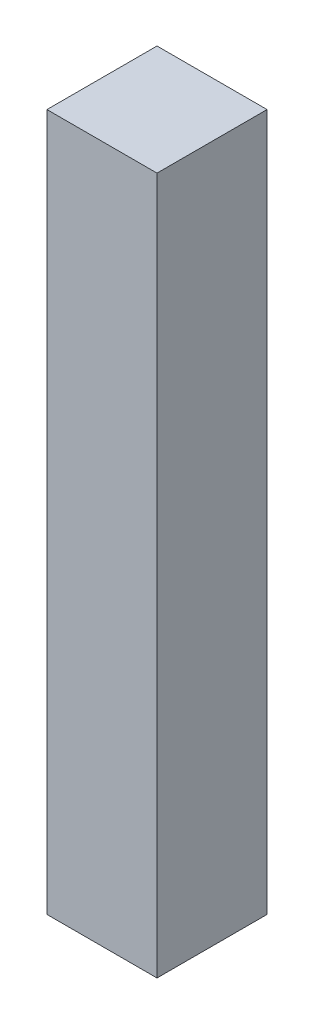
SolidWorks part; units mm, degrees
material "Cedar"
ref_plane "Front" through (0, 0, 0) normal (0, 0, 1) x (1, 0, 0)
ref_plane "Top" through (0, 0, 0) normal (0, 1, 0) x (1, 0, 0)
ref_plane "Right" through (0, 0, 0) normal (1, 0, 0) x (0, 0, -1)
sketch "Sketch1" plane through (0, 0, 0) normal (0, 1, 0) x (1, 0, 0)
  line L1 (-15, -15) -> (15, -15)
  line L2 (-15, -15) -> (-15, 15)
  line L3 (-15, 15) -> (15, 15)
  line L4 (15, -15) -> (15, 15)
  line L5 (-15, -15) -> (15, 15) construction
  line L6 (-15, 15) -> (15, -15) construction
  point P0 (0, 0)
  dimension "D1" = 30
  dimension "D2" = 30
extrude "Boss-Extrude1" add sketch "Sketch1" along normal blind 190
